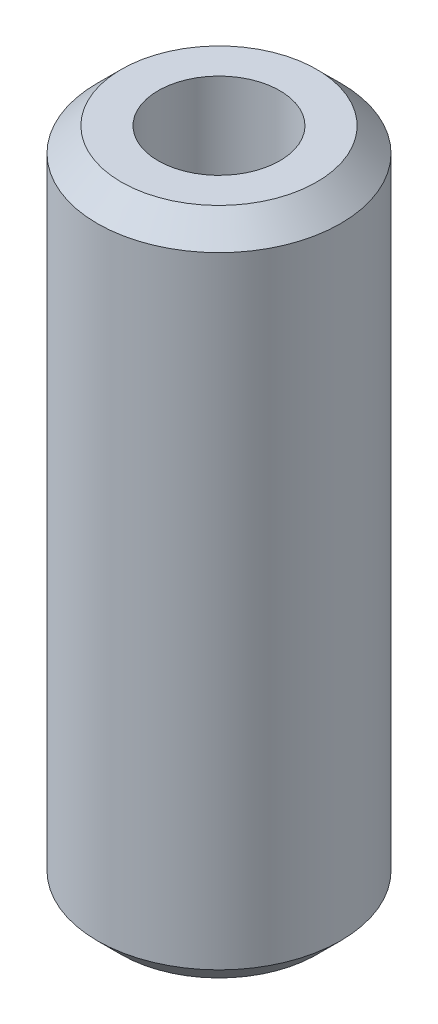
SolidWorks part; units mm, degrees
ref_plane "Alzado" through (0, 0, 0) normal (0, 0, 1) x (1, 0, 0)
ref_plane "Planta" through (0, 0, 0) normal (0, 1, 0) x (1, 0, 0)
ref_plane "Vista lateral" through (0, 0, 0) normal (1, 0, 0) x (0, 0, -1)
sketch "Croquis2" plane through (0, 0, 0) normal (0, 1, 0) x (1, 0, 0)
  circle A0 centre (0, 0) radius 6.35
  circle A1 centre (0, 0) radius 12.7
  dimension "D1" = 12.7
  dimension "D2" = 25.4
extrude "Saliente-Extruir1" add sketch "Croquis2" along normal mid plane 69.85
chamfer "Chaflán1" distance 2.5 angle 45 2 edges at (0, -34.925, 12.7) (0, 34.925, 12.7)
